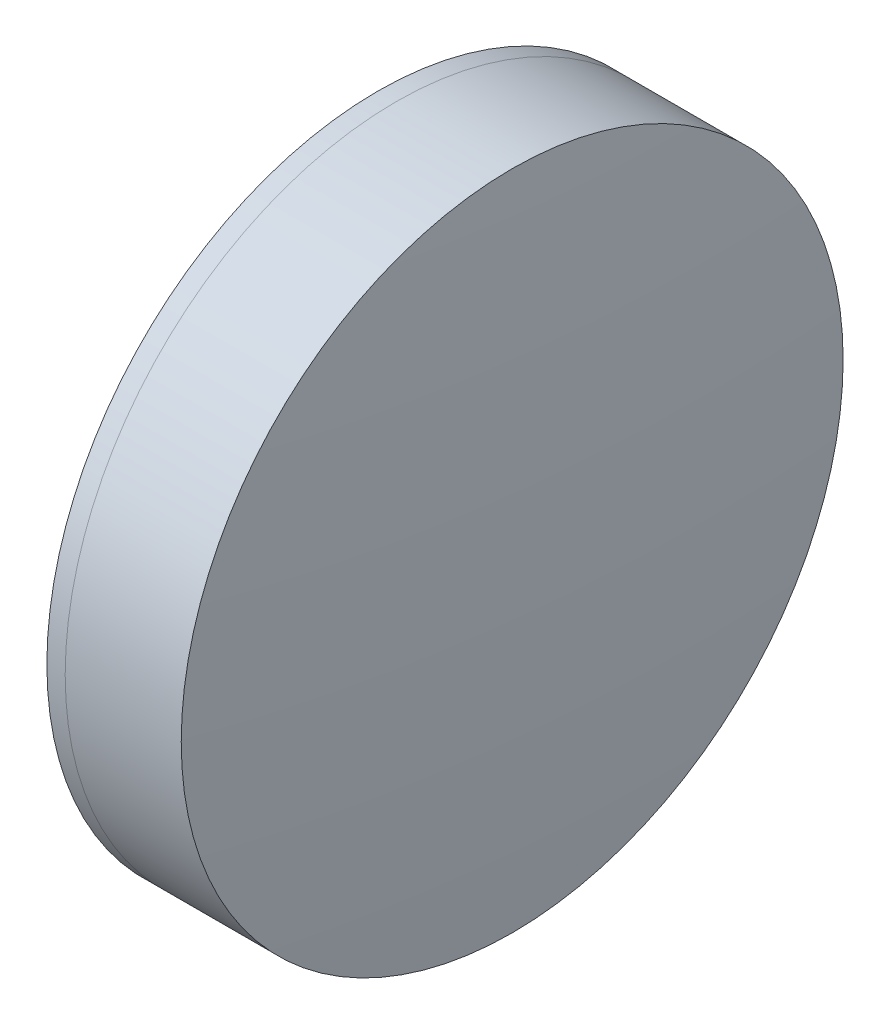
SolidWorks part; units mm, degrees
ref_plane "前视基准面" through (0, 0, 0) normal (0, 0, 1) x (1, 0, 0)
ref_plane "上视基准面" through (0, 0, 0) normal (0, 1, 0) x (1, 0, 0)
ref_plane "右视基准面" through (0, 0, 0) normal (1, 0, 0) x (0, 0, -1)
sketch "草图1" plane through (0, 0, 0) normal (0, 1, 0) x (1, 0, 0)
  line L0 (124.5233, 0) -> (646.9917, 0) construction
  line L1 (521.4133, -25.4) -> (522.819, -25.4)
  line L2 (521.4133, 25.4) -> (522.819, 25.4)
  arc A0 (522.819, -25.4) -> (522.819, 25.4) centre (486.1584, 0) ccw
  arc A1 (521.4133, 25.4) -> (521.4133, -25.4) centre (566.5584, 0) ccw
  point P10 (514.7584, 0)
  point P11 (530.7584, 0)
  dimension "D3" = 51.8
  dimension "D4" = 44.6
  dimension "D1" = 25.4
  dimension "D2" = 25.4
  dimension "D5" = 16
revolve "旋转1" add sketch "草图1" angle 360 about L0
sketch "草图2" plane through (0, 0, 0) normal (0, 1, 0) x (1, 0, 0)
  line L0 (-0.5519, 0) -> (622.6607, 0) construction
  line L2 (522.819, 25.4) -> (531.7248, 25.4)
  line L3 (522.819, -25.4) -> (531.7248, -25.4)
  arc A0 (531.7248, -25.4) -> (531.7248, 25.4) centre (220.1584, 0) ccw
  arc A1 (522.819, -25.4) -> (522.819, 25.4) centre (486.1584, 0) ccw construction
  arc A2 (522.819, -25.4) -> (522.819, 25.4) centre (486.1584, 0) ccw
  point P4 (530.7584, 0)
  point P8 (532.7584, 0)
  dimension "D1" = 312.6
  dimension "D2" = 2
revolve "旋转3" add sketch "草图2" angle 360 about L0
